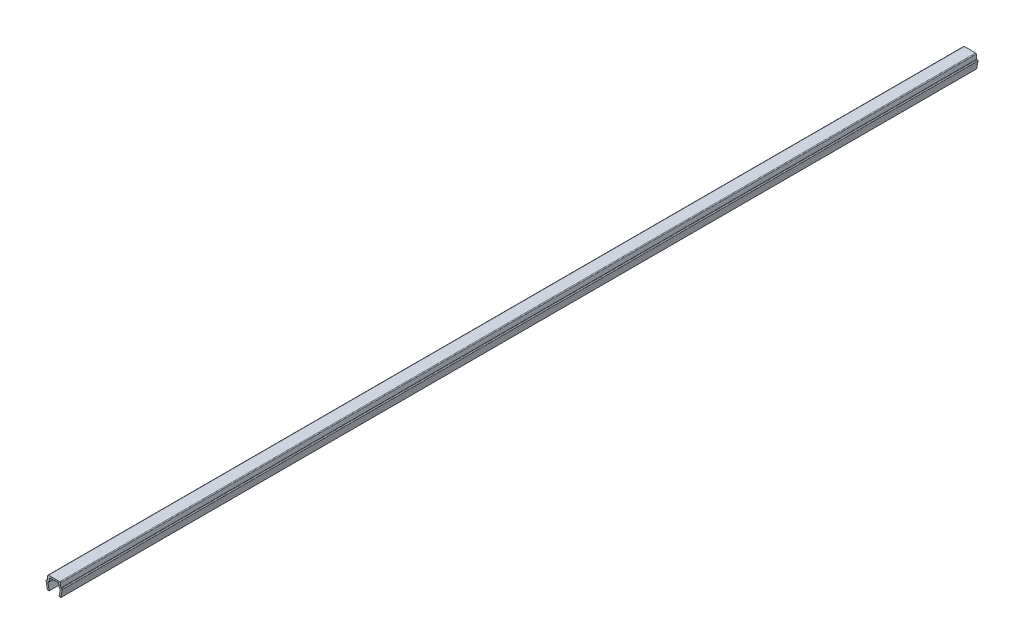
SolidWorks part; units mm, degrees
ref_plane "Front Plane" through (0, 0, 0) normal (0, 0, 1) x (1, 0, 0)
ref_plane "Top Plane" through (0, 0, 0) normal (0, 1, 0) x (1, 0, 0)
ref_plane "Right Plane" through (0, 0, 0) normal (1, 0, 0) x (0, 0, -1)
ref_plane "Plane1" through (0, 0, 0) normal (0, 0, 1) x (1, 0, 0)
sketch "Sketch1" plane through (0, 0, 0) normal (0, 0, 1) x (1, 0, 0)
  line L0 (-3.6, 3.35) -> (-3, 0)
  line L1 (-3, 0) -> (-2.2, 0)
  line L2 (-2.2, 0) -> (-2.7352, 2.9883)
  line L3 (-2.3907, 3.4) -> (-2.2, 3.4)
  line L4 (-2.2, 3.4) -> (-2.0705, 4.8805)
  line L5 (-1.7218, 5.2) -> (1.7218, 5.2)
  line L6 (2.0705, 4.8805) -> (2.2, 3.4)
  line L7 (2.2, 3.4) -> (2.3907, 3.4)
  line L8 (2.7352, 2.9883) -> (2.2, 0)
  line L9 (2.2, 0) -> (3, 0)
  line L10 (3, 0) -> (3.6, 3.35)
  line L11 (3.25, 3.7) -> (3, 3.7)
  line L12 (3, 3.7) -> (2.8355, 5.5805)
  line L13 (2.4868, 5.9) -> (-2.4868, 5.9)
  line L14 (-2.8355, 5.5805) -> (-3, 3.7)
  line L15 (-3, 3.7) -> (-3.25, 3.7)
  arc A0 (-2.7352, 2.9883) -> (-2.3907, 3.4) centre (-2.3907, 3.05) cw
  arc A1 (-2.0705, 4.8805) -> (-1.7218, 5.2) centre (-1.7218, 4.85) cw
  arc A2 (1.7218, 5.2) -> (2.0705, 4.8805) centre (1.7218, 4.85) cw
  arc A3 (2.3907, 3.4) -> (2.7352, 2.9883) centre (2.3907, 3.05) cw
  arc A4 (3.6, 3.35) -> (3.25, 3.7) centre (3.25, 3.35) ccw
  arc A5 (2.8355, 5.5805) -> (2.4868, 5.9) centre (2.4868, 5.55) ccw
  arc A6 (-2.4868, 5.9) -> (-2.8355, 5.5805) centre (-2.4868, 5.55) ccw
  arc A7 (-3.25, 3.7) -> (-3.6, 3.35) centre (-3.25, 3.35) ccw
extrude "Boss-Extrude1" add sketch "Sketch1" against normal mid plane 407.5
